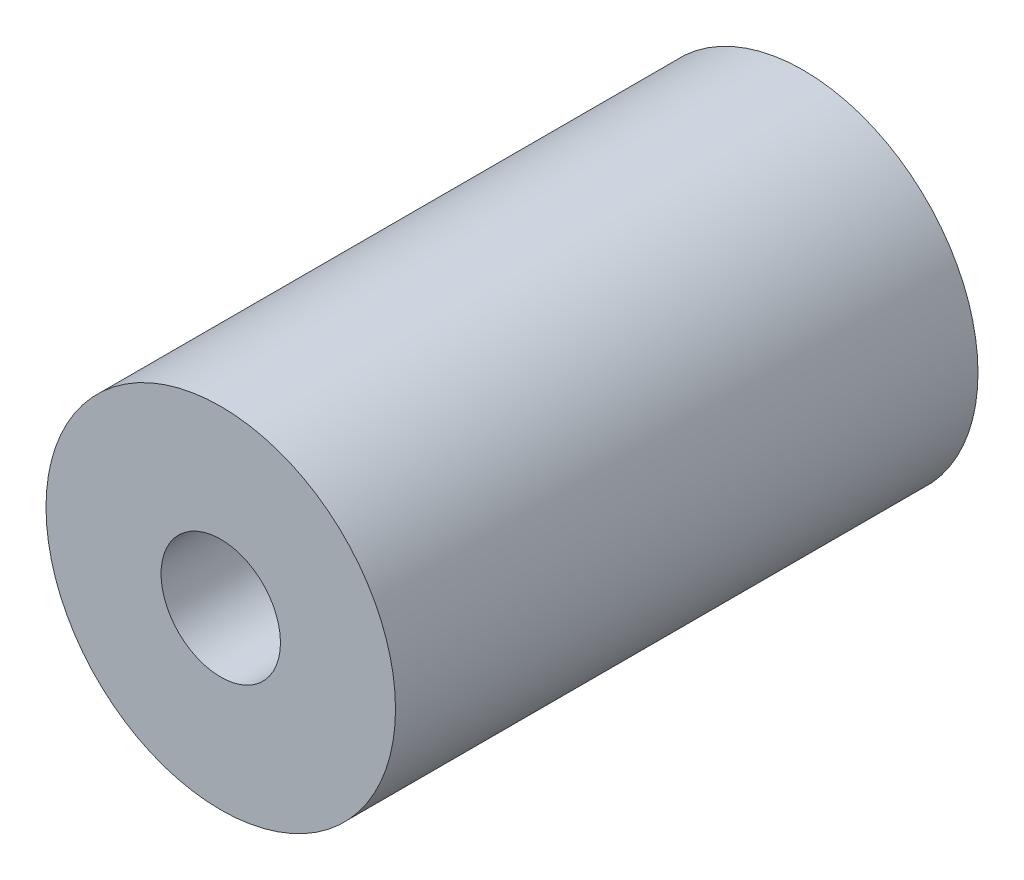
SolidWorks part; units mm, degrees
ref_plane "Front" through (0, 0, 0) normal (0, 0, 1) x (1, 0, 0)
ref_plane "Top" through (0, 0, 0) normal (0, 1, 0) x (1, 0, 0)
ref_plane "Right" through (0, 0, 0) normal (1, 0, 0) x (0, 0, -1)
sketch "Sketch1" plane through (0, 0, 0) normal (0, 0, 1) x (1, 0, 0)
  circle A0 centre (0, 0) radius 3
  dimension "D1" = 6
extrude "Boss-Extrude1" add sketch "Sketch1" along normal blind 10
hole_wizard "M2.5 Tapped Hole1" positions "3DSketch2" profile "Sketch3" tap size "M2.5" standard "ISO" end condition through all
sketch3d "3DSketch2"
  line L0 (0, 0, 10) -> (0, 0, 0) construction
  point P0 (0, 0, 10)
sketch "Sketch3" plane through (0, 0, 10) normal (1, 0, 0) x (0, -1, 0)
  line L0 (0, 0) -> (0, 10)
  line L1 (0, 10) -> (1.025, 10)
  line L2 (1.025, 10) -> (1.025, 0)
  line L5 (1.025, 0) -> (0, 0)
  line L11 (0, -6.35) -> (0, 107.95) construction
  dimension "Thru Tap Drill Dia." = 2.05
  dimension "Thru Tap Drill Depth" = 10
cosmetic thread "Hole Thread1" parameters "D2"=2.5
